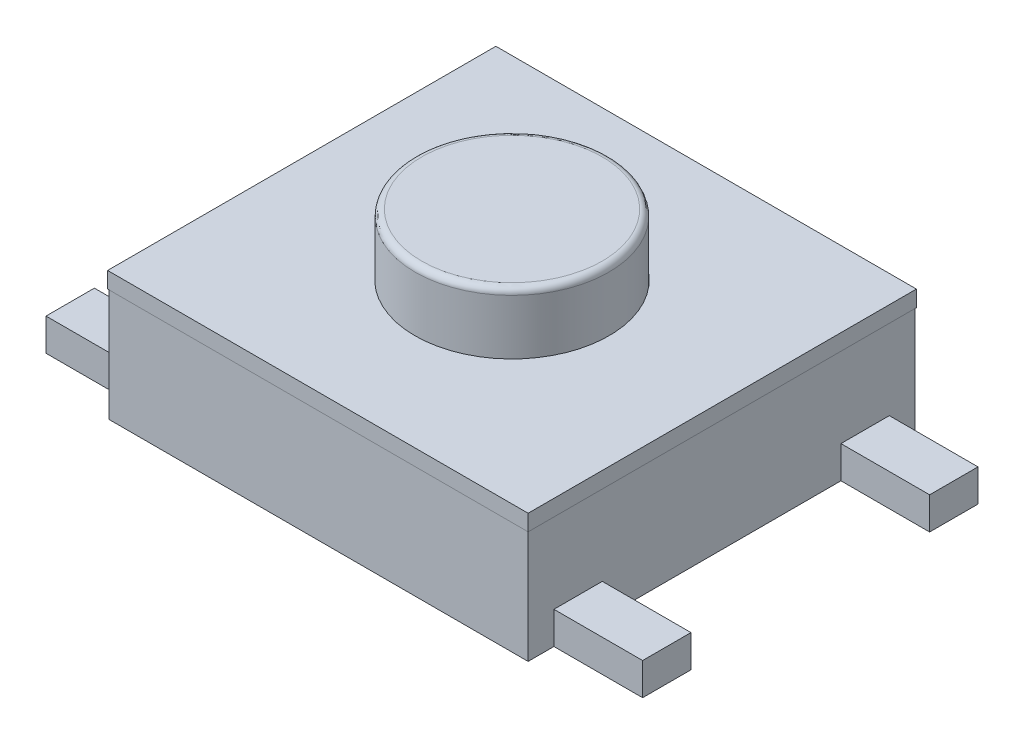
SolidWorks part; units mm, degrees
ref_plane "Front" through (0, 0, 0) normal (0, 0, 1) x (1, 0, 0)
ref_plane "Top" through (0, 0, 0) normal (0, 1, 0) x (1, 0, 0)
ref_plane "Right" through (0, 0, 0) normal (1, 0, 0) x (0, 0, -1)
sketch "Sketch1" plane through (0, 0, 0) normal (0, 1, 0) x (1, 0, 0)
  line L0 (-3.25, -3) -> (3.25, 3) construction
  line L1 (-3.25, 3) -> (3.25, 3)
  line L2 (-3.25, 3) -> (-3.25, -3)
  line L3 (-3.25, -3) -> (3.25, -3)
  line L4 (3.25, 3) -> (3.25, -3)
  point P4 (0, 0)
  dimension "D1" = 6
  dimension "D2" = 6.5
extrude "Boss-Extrude1" add sketch "Sketch1" along normal blind 1.75
sketch "Sketch2" plane through (0, 1.75, 0) normal (0, 1, 0) x (1, 0, 0)
  line L8 (-3.26, 3.01) -> (-3.26, -3.01)
  line L9 (-3.26, -3.01) -> (3.26, -3.01)
  line L10 (3.26, -3.01) -> (3.26, 3.01)
  line L11 (3.26, 3.01) -> (-3.26, 3.01)
  line L12 (-3.26, 3.01) -> (-3.26, -3.01)
  line L13 (-3.26, -3.01) -> (3.26, -3.01)
  line L14 (3.26, -3.01) -> (3.26, 3.01)
  line L15 (3.26, 3.01) -> (-3.26, 3.01)
  circle A0 centre (0, 0) radius 1.505
  dimension "D2" = 3.01
  dimension "D1" = 0.01
extrude "Boss-Extrude2" add sketch "Sketch2" along normal blind 0.25
sketch "Sketch3" plane through (0, 1.75, 0) normal (0, 1, 0) x (1, 0, 0)
  circle A0 centre (0, 0) radius 1.5
  dimension "D1" = 3
extrude "Boss-Extrude3" add sketch "Sketch3" along normal blind 1.2
fillet "Fillet1" radius 0.1 1 edges at (0, 2.95, 1.5)
sketch "Sketch4" plane through (0, 0, 0) normal (0, -1, 0) x (1, 0, 0)
  line L0 (0, 2.1439) -> (0, 0) construction
  line L1 (0, 0) -> (3.9752, 0) construction
  line L2 (3.25, 3) -> (3.25, -3) construction
  line L3 (3.25, 2.6) -> (4.625, 2.6)
  line L4 (3.25, 2.6) -> (3.25, 1.85)
  line L5 (3.25, 1.85) -> (4.625, 1.85)
  line L6 (4.625, 2.6) -> (4.625, 1.85)
  line L8 (4.625, -2.6) -> (4.625, -1.85)
  line L9 (3.25, -1.85) -> (4.625, -1.85)
  line L10 (3.25, -2.6) -> (3.25, -1.85)
  line L11 (3.25, -2.6) -> (4.625, -2.6)
  line L12 (-3.25, -2.6) -> (-4.625, -2.6)
  line L13 (-3.25, -2.6) -> (-3.25, -1.85)
  line L14 (-3.25, -1.85) -> (-4.625, -1.85)
  line L15 (-4.625, -2.6) -> (-4.625, -1.85)
  line L16 (-4.625, 2.6) -> (-4.625, 1.85)
  line L17 (-3.25, 1.85) -> (-4.625, 1.85)
  line L18 (-3.25, 2.6) -> (-3.25, 1.85)
  line L19 (-3.25, 2.6) -> (-4.625, 2.6)
  line L20 (-3.25, -3) -> (-3.25, 3) construction
  line L21 (-3.25, 0.375) -> (-4.625, 0.375)
  line L22 (-3.25, 0.375) -> (-3.25, -0.375)
  line L23 (-3.25, -0.375) -> (-4.625, -0.375)
  line L24 (-4.625, 0.375) -> (-4.625, -0.375)
  point P28 (-3.25, 0)
  dimension "D1" = 0.75
  dimension "D2" = 5.2
  dimension "D3" = 9.25
extrude "Boss-Extrude4" add sketch "Sketch4" against normal blind 0.5
